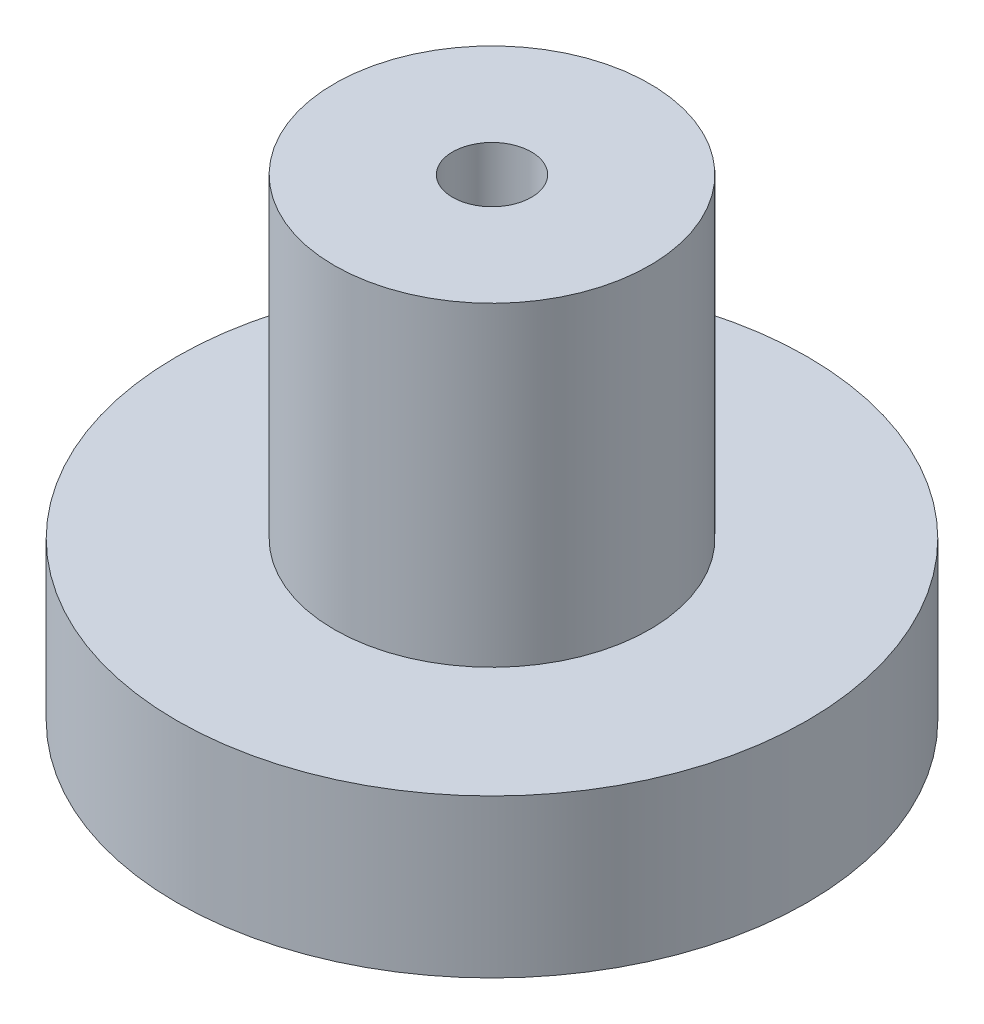
SolidWorks part; units mm, degrees
ref_plane "Front Plane" through (0, 0, 0) normal (0, 0, 1) x (1, 0, 0)
ref_plane "Top Plane" through (0, 0, 0) normal (0, 1, 0) x (1, 0, 0)
ref_plane "Right Plane" through (0, 0, 0) normal (1, 0, 0) x (0, 0, -1)
sketch "Sketch1" plane through (0, 0, 0) normal (0, 1, 0) x (1, 0, 0)
  circle A0 centre (0, 0) radius 3.175
  dimension "D1" = 6.35
extrude "Boss-Extrude1" add sketch "Sketch1" along normal blind 4.7625
sketch "Sketch2" plane through (0, 4.7625, 0) normal (0, 1, 0) x (1, 0, 0)
  circle A0 centre (0, 0) radius 3.175
  circle A1 centre (0, 0) radius 1.5875
  circle M1 centre (0, 0) radius 3.175
  dimension "D1" = 3.175
extrude "Cut-Extrude1" cut sketch "Sketch2" against normal blind 3.175 contours A1 M1
sketch "Sketch3" plane through (0, 4.7625, 0) normal (0, 1, 0) x (1, 0, 0)
  circle A0 centre (0, 0) radius 0.3969
  dimension "D1" = 0.7937
extrude "Cut-Extrude2" cut sketch "Sketch3" against normal through all
sketch "Sketch4" plane through (0, 0, 0) normal (1, 0, 0) x (0, 0, -1)
  line L0 (0, 0) -> (0, 0.7937)
  line L1 (0, 0.7937) -> (-0.7937, 0)
  line L2 (-0.7937, 0) -> (0, 0)
  dimension "D1" = 0.7937
  dimension "D2" = 0.7937
revolve "Cut-Revolve1" cut sketch "Sketch4" angle 360 about L0
